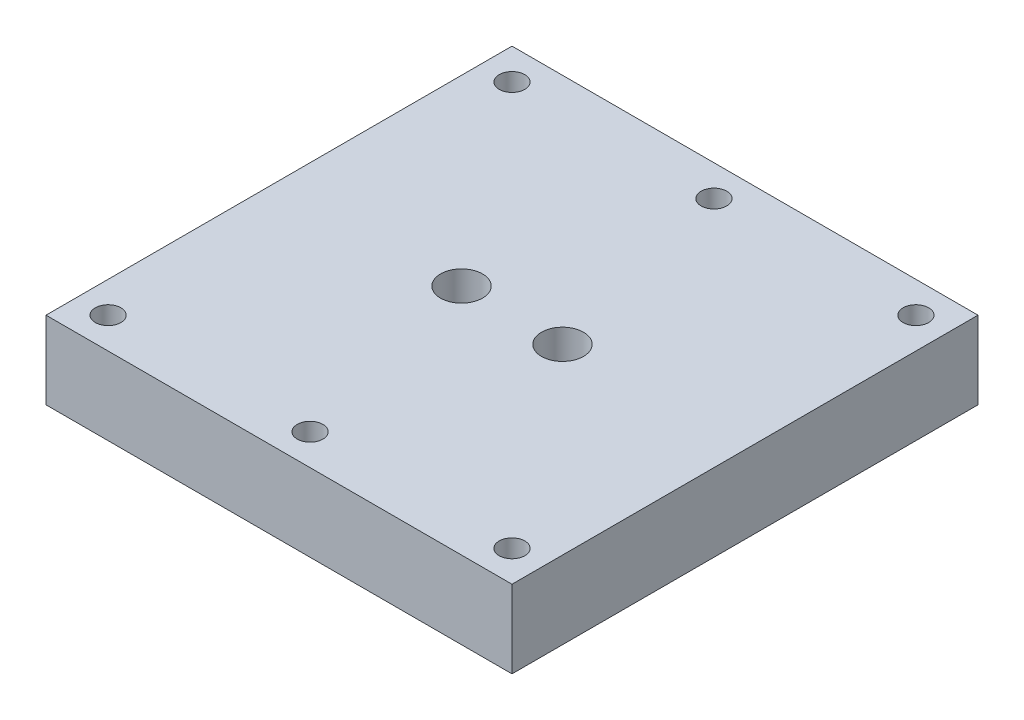
SolidWorks part; units mm, degrees
ref_plane "Front Plane" through (0, 0, 0) normal (0, 0, 1) x (1, 0, 0)
ref_plane "Top Plane" through (0, 0, 0) normal (0, 1, 0) x (1, 0, 0)
ref_plane "Right Plane" through (0, 0, 0) normal (1, 0, 0) x (0, 0, -1)
sketch "Sketch2" plane through (0, 0, 0) normal (0, 1, 0) x (1, 0, 0)
  line L1 (30, -30) -> (-30, -30)
  line L2 (30, -30) -> (30, 30)
  line L3 (30, 30) -> (-30, 30)
  line L4 (-30, -30) -> (-30, 30)
  line L5 (30, -30) -> (-30, 30) construction
  line L6 (30, 30) -> (-30, -30) construction
  point P0 (0, 0)
  dimension "D1" = 60
  dimension "D2" = 60
extrude "Boss-Extrude1" add sketch "Sketch2" along normal blind 10
hole_wizard "Tap Drill for M4x0.7 Tap1" positions "Sketch8" profile "Sketch7" hole size "M4x0.7" standard "ANSI Metric" end condition up to next
sketch "Sketch8" plane through (0, 0, 0) normal (0, -1, 0) x (-1, 0, 0)
  line L0 (0, 30) -> (0, -30) construction
  line L1 (-30, 30) -> (30, 30) construction
  line L2 (30, -30) -> (-30, -30) construction
  line L4 (30, 0) -> (-30, 0) construction
  line L5 (30, 30) -> (30, -30) construction
  line L6 (-30, -30) -> (-30, 30) construction
  line L7 (0, 26) -> (26, 26) construction
  point P23 (0, 26)
  point P29 (26, 26)
  point P32 (-26, 26)
  point P33 (-26, -26)
  point P34 (0, -26)
  point P35 (26, -26)
  dimension "D1" = 4
  dimension "D3" = 26
  dimension "D2" = 2
sketch "Sketch7" plane through (0, 0, -26) normal (1, 0, 0) x (0, 0, -1)
  line L0 (0, 0) -> (0, 10)
  line L1 (0, 10) -> (1.65, 10)
  line L2 (1.65, 10) -> (1.65, 0)
  line L5 (1.65, 0) -> (0, 0)
  line L11 (0, -6.35) -> (0, 107.95) construction
  dimension "Thru Hole Dia." = 3.3
  dimension "Thru Hole Depth" = 10
hole_wizard "1/4-28 Tapped Hole5" positions "Sketch24" profile "Sketch23" tap size "1/4-28" standard "ANSI Inch"
sketch "Sketch24" plane through (0, 10, 0) normal (0, -1, 0) x (-1, 0, 0)
  line L2 (0, 30) -> (0, -30) construction
  line L3 (-30, 30) -> (30, 30) construction
  line L4 (30, -30) -> (-30, -30) construction
  line L6 (30, 0) -> (-30, 0) construction
  line L7 (30, 30) -> (30, -30) construction
  line L8 (-30, -30) -> (-30, 30) construction
  point P21 (6.5, 0)
  point P25 (-6.5, 0)
  dimension "D1" = 6.5
sketch "Sketch23" plane through (-6.5, 10, 0) normal (1, 0, 0) x (0, 0, 1)
  line L0 (0, 0) -> (0, 8.6254)
  line L1 (0, 8.6254) -> (2.7051, 7)
  line L2 (2.7051, 7) -> (2.7051, 0)
  line L5 (2.7051, 0) -> (0, 0)
  line L10 (0, 8.6254) -> (-2.7051, 7) construction
  line L11 (0, -6.35) -> (0, 107.95) construction
  dimension "Tap Drill Dia." = 5.4102
  dimension "Tap Drill Depth" = 7
  dimension "Drill Angle" = 118
cosmetic thread "Hole Thread1"
cosmetic thread "Hole Thread2"
hole_wizard "Ø1.0mm Dowel Hole1" positions "Sketch26" profile "Sketch25" hole size "Ø1.0" standard "ANSI Metric" end condition through all
sketch "Sketch26" plane through (0, 10, 0) normal (0, 1, 0) x (1, 0, 0)
  point P0 (-6.5, 0)
  point P3 (6.5, 0)
sketch "Sketch25" plane through (-6.5, 10, 0) normal (1, 0, 0) x (0, 0, 1)
  line L0 (0, 0) -> (0, 10)
  line L1 (0, 10) -> (0.5, 10)
  line L2 (0.5, 10) -> (0.5, 0)
  line L5 (0.5, 0) -> (0, 0)
  line L11 (0, -6.35) -> (0, 107.95) construction
  dimension "Thru Hole Dia." = 1
  dimension "Thru Hole Depth" = 10
